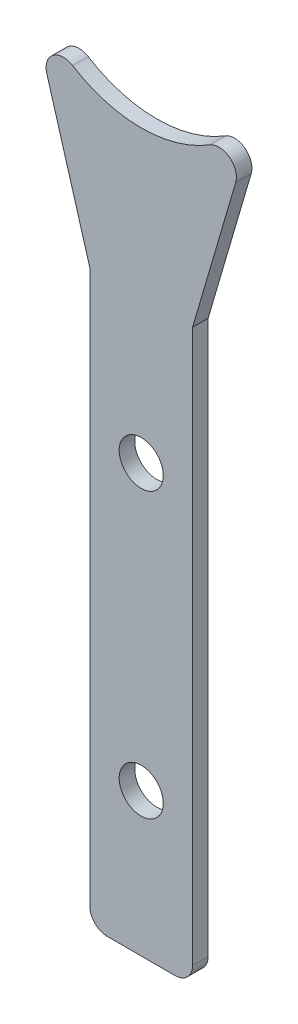
SolidWorks part; units mm, degrees
material "ASTM A36 Steel"
ref_plane "X-Y Datum" through (0, 0, 0) normal (0, 0, 1) x (1, 0, 0)
ref_plane "X-Z Datum" through (0, 0, 0) normal (0, 1, 0) x (1, 0, 0)
ref_plane "Y-Z Datum" through (0, 0, 0) normal (1, 0, 0) x (0, 0, -1)
sketch "Sketch1" plane through (0, 0, 0) normal (0, 0, 1) x (1, 0, 0)
  line L0 (2.16, -14.0069) -> (2.16, -28.6179)
  line L2 (-3.0789, -28.6179) -> (-3.0789, 29.5681)
  line L5 (-3.0789, -28.6179) -> (7.3993, -28.6179)
  line L6 (-3.0789, 29.5681) -> (2.16, 29.5681)
  line L7 (7.3993, -28.6179) -> (7.3993, 14.5674)
  line L8 (-3.0789, 29.5681) -> (-9.5797, 51.7194)
  line L9 (7.3993, 14.5674) -> (7.3993, 29.5674)
  line L11 (7.3993, 29.5674) -> (13.8976, 51.7194)
  circle A5 centre (2.159, 57.7781) radius 13.21
  circle A6 centre (2.16, 14.9571) radius 2
  circle A7 centre (2.16, -14.0069) radius 2
  point P0 (0, 0)
  dimension "D1" = 26.42
  dimension "D2" = 4
  dimension "D3" = 4
  dimension "D6" = 28.21
  dimension "D4" = 28.964
  dimension "D5" = 14.611
extrude "Boss-Extrude1" add sketch "Sketch1" along normal blind 1.5875
fillet "Fillet2" radius 1.778 4 edges at (7.3993, -28.6179, 0.7937) (-3.0789, -28.6179, 0.7937) (-9.5797, 51.7194, 0.7937) (13.8976, 51.7194, 0.7937)
hole_wizard "M4 Clearance Hole2" positions "Sketch4" profile "Sketch5" hole size "M4" standard "ANSI Metric" end condition through all
sketch "Sketch4" plane through (0, 0, 1.5875) normal (0, 0, 1) x (1, 0, 0)
  point P0 (2.16, 14.9571)
  point P3 (2.16, -14.0069)
sketch "Sketch5" plane through (2.16, 14.9571, 1.5875) normal (1, 0, 0) x (0, -1, 0)
  line L0 (0, 0) -> (0, 1.5875)
  line L1 (0, 1.5875) -> (2.25, 1.5875)
  line L2 (2.25, 1.5875) -> (2.25, 0)
  line L5 (2.25, 0) -> (0, 0)
  line L11 (0, -6.35) -> (0, 107.95) construction
  dimension "Thru Hole Dia." = 4.5
  dimension "Thru Hole Depth" = 1.5875
